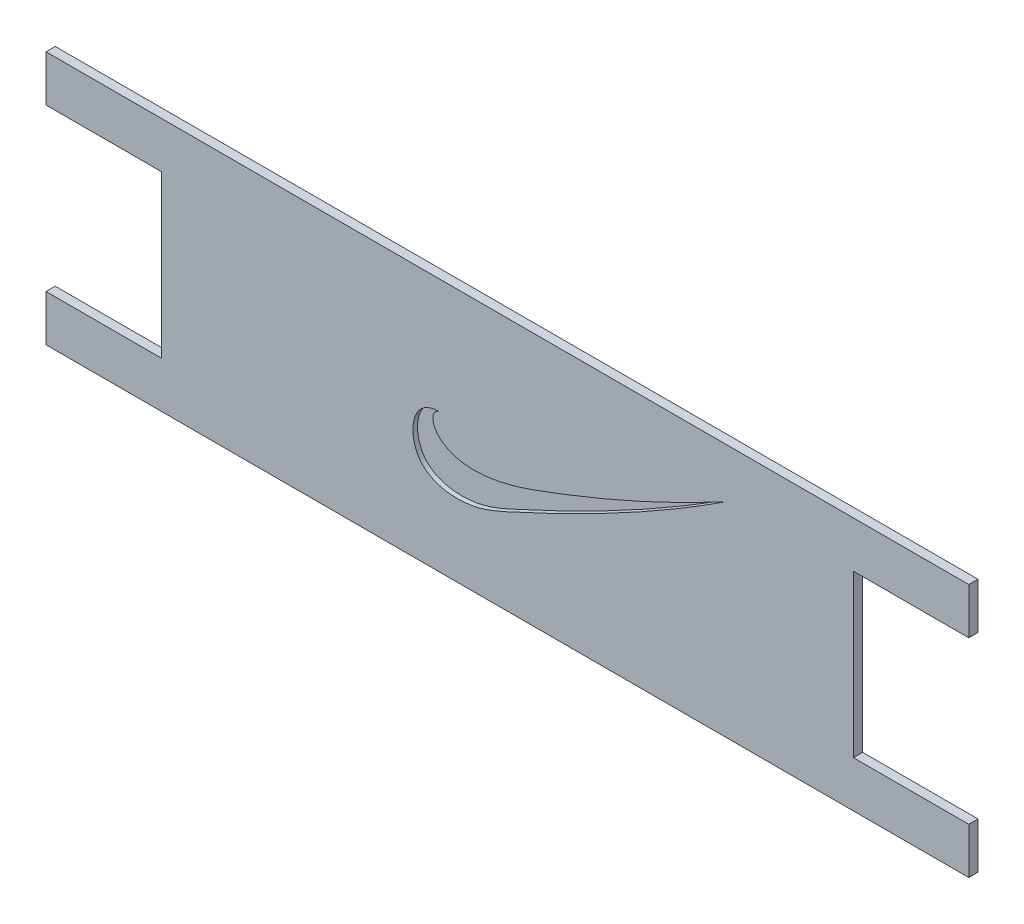
SolidWorks part; units mm, degrees
ref_plane "Front Plane" through (0, 0, 0) normal (0, 0, 1) x (1, 0, 0)
ref_plane "Top Plane" through (0, 0, 0) normal (0, 1, 0) x (1, 0, 0)
ref_plane "Right Plane" through (0, 0, 0) normal (1, 0, 0) x (0, 0, -1)
sketch "Sketch1" plane through (0, 0, 0) normal (0, 0, 1) x (1, 0, 0)
  line L1 (-48.3108, 14.244) -> (151.6892, 14.244)
  line L2 (-48.3108, 14.244) -> (-48.3108, 4.244)
  line L3 (-48.3108, -40.756) -> (151.6892, -40.756)
  line L4 (151.6892, 14.244) -> (151.6892, 4.244)
  line L5 (-23.3108, 4.244) -> (-48.3108, 4.244)
  line L6 (-48.3108, -30.756) -> (-23.3108, -30.756)
  line L9 (126.6892, 4.244) -> (151.6892, 4.244)
  line L10 (-23.3108, 4.244) -> (-23.3108, -30.756)
  line L11 (-48.3108, -30.756) -> (-48.3108, -40.756)
  line L13 (126.6892, -30.756) -> (151.6892, -30.756)
  line L14 (126.6892, 4.244) -> (126.6892, -30.756)
  line L15 (151.6892, -30.756) -> (151.6892, -40.756)
  dimension "D1" = 55
  dimension "D2" = 200
  dimension "D3" = 10
  dimension "D5" = 10
extrude "Boss-Extrude1" add sketch "Sketch1" along normal blind 2
sketch "Sketch3" plane through (0, 0, 2) normal (0, 0, 1) x (1, 0, 0)
  line L1 (51.6892, 36.8392) -> (51.6892, -73.5664) construction
  spline S0 degree 3 poles (37.1895, -10.7183) (33.4742, -10.6242) (35.3006, -23.2165) (74.22, -9.0463) (87.6649, -2.595) (98.8534, 3.3374) knots 0 0 0 0 0.517765 0.59262 1 1 1 1
  spline S1 degree 3 poles (37.1895, -10.7183) (30.8159, -10.3327) (29.1569, -24.1699) (43.2502, -25.8533) (65.1902, -16.1789) (83.9965, -6.3848) (98.8534, 3.3374) knots 0 0 0 0 0.163171 0.291764 0.388322 1 1 1 1
  dimension "D1" = 100
extrude "Cut-Extrude1" cut sketch "Sketch3" against normal blind 1
scale "Scale1" bodies to scale 102 scale about centroid uniform scaling yes scale factor 0.5
